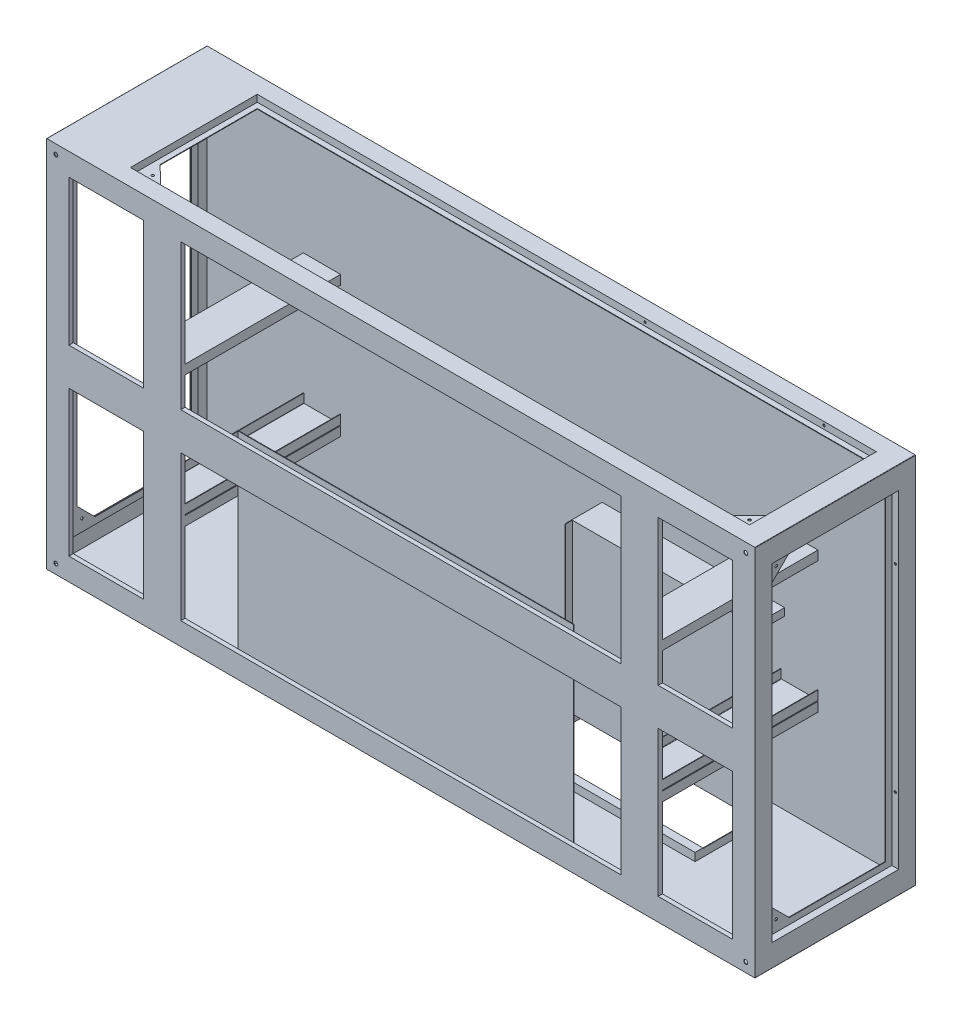
SolidWorks part; units mm, degrees
ref_plane "前视基准面" through (0, 0, 0) normal (0, 0, 1) x (1, 0, 0)
ref_plane "上视基准面" through (0, 0, 0) normal (0, 1, 0) x (1, 0, 0)
ref_plane "右视基准面" through (0, 0, 0) normal (1, 0, 0) x (0, 0, -1)
sketch "草图1" plane through (0, 0, 0) normal (0, 0, 1) x (1, 0, 0)
  line L1 (950, -500) -> (-950, -500)
  line L2 (950, -500) -> (950, 500)
  line L3 (950, 500) -> (-950, 500)
  line L4 (-950, -500) -> (-950, 500)
  line L5 (950, -500) -> (-950, 500) construction
  line L6 (950, 500) -> (-950, -500) construction
  line L7 (948.5, -498.5) -> (-948.5, -498.5)
  line L8 (948.5, -498.5) -> (948.5, 498.5)
  line L9 (948.5, 498.5) -> (-948.5, 498.5)
  line L10 (-948.5, -498.5) -> (-948.5, 498.5)
  line L11 (948.5, -498.5) -> (-948.5, 498.5) construction
  line L12 (948.5, 498.5) -> (-948.5, -498.5) construction
  point P0 (0, 0)
  point P6 (0, 0)
  dimension "D1" = 1.5
  dimension "D2" = 1.5
  dimension "D3" = 1900
  dimension "D4" = 1000
extrude "凸台-拉伸1" add sketch "草图1" along normal mid plane 430
sketch "草图2" plane through (0, 0, -215) normal (0, 0, -1) x (-1, 0, 0)
  line L1 (-950, 500) -> (950, 500)
  line L2 (-950, 500) -> (-950, -500)
  line L3 (-950, -500) -> (950, -500)
  line L4 (950, 500) -> (950, -500)
  line L5 (-950, 500) -> (950, -500) construction
  line L6 (-950, -500) -> (950, 500) construction
  point P0 (0, 0)
extrude "凸台-拉伸2" add sketch "草图2" against normal blind 1.5
sketch "草图3" plane through (-950, 0, 0) normal (-1, 0, 0) x (0, 0, 1)
  line L0 (215, -500) -> (-215, -500) construction
  line L1 (-170, -440) -> (170, -440)
  line L2 (-170, -440) -> (-170, 440)
  line L3 (-170, 440) -> (170, 440)
  line L4 (170, -440) -> (170, 440)
  line L5 (-170, -440) -> (170, 440) construction
  line L6 (-170, 440) -> (170, -440) construction
  line L7 (-215, 500) -> (-215, -500) construction
  point P0 (0, 0)
  dimension "D1" = 60
  dimension "D2" = 45
extrude "切除-拉伸1" cut sketch "草图3" against normal blind 1.5
sketch "草图6" plane through (0, 0, 215) normal (0, 0, 1) x (1, 0, 0)
  line L0 (950, 500) -> (-950, 500) construction
  line L1 (-950, -500) -> (950, -500)
  line L2 (-950, -500) -> (-950, 500)
  line L3 (-950, 500) -> (950, 500)
  line L4 (950, -500) -> (950, 500)
  line L5 (-950, -500) -> (950, 500) construction
  line L6 (-950, 500) -> (950, -500) construction
  line L7 (-950, 500) -> (-950, -500) construction
  point P0 (0, 0)
extrude "凸台-拉伸5" add sketch "草图6" against normal blind 1.5
sketch "草图7" plane through (0, 0, 227) normal (0, 0, 1) x (1, 0, 0)
  line L0 (0, 500) -> (0, -500) construction
  line L1 (-890, -440) -> (-690, -440)
  line L2 (-890, -440) -> (-890, 440)
  line L3 (-890, 440) -> (-690, 440)
  line L4 (-690, -440) -> (-690, 440)
  line L5 (-890, -440) -> (-690, 440) construction
  line L6 (-890, 440) -> (-690, -440) construction
  line L7 (-590, -440) -> (590, -440)
  line L8 (-590, -440) -> (-590, 440)
  line L9 (-590, 440) -> (590, 440)
  line L10 (590, -440) -> (590, 440)
  line L11 (-590, -440) -> (590, 440) construction
  line L12 (-590, 440) -> (590, -440) construction
  line L13 (690, -440) -> (890, -440)
  line L14 (690, -440) -> (690, 440)
  line L15 (690, 440) -> (890, 440)
  line L16 (890, -440) -> (890, 440)
  line L17 (690, -440) -> (890, 440) construction
  line L18 (690, 440) -> (890, -440) construction
  line L19 (945, 500) -> (-945, 500) construction
  line L20 (-945, -500) -> (945, -500) construction
  line L21 (-400, 0) -> (950, 0) construction
  line L22 (-950, 495) -> (-950, -495) construction
  line L23 (950, -495) -> (950, 495) construction
  point P0 (-790, 0)
  point P5 (0, 0)
  point P10 (790, 0)
  dimension "D1" = 60
  dimension "D2" = 60
  dimension "D3" = 60
  dimension "D4" = 60
  dimension "D5" = 100
  dimension "D6" = 200
extrude "切除-拉伸8" cut sketch "草图7" against normal blind 29.5
hole_wizard "Ø10.5 (10.5) 直径孔1" positions "草图9" profile "草图8" hole size "Ø10.5" standard "GB"
sketch "草图9" plane through (0, 0, 215) normal (0, 0, 1) x (1, 0, 0)
  line L0 (950, 500) -> (-950, 500) construction
  line L1 (-950, 500) -> (-950, -500) construction
  line L2 (950, -500) -> (950, 500) construction
  line L3 (-950, -500) -> (950, -500) construction
  point P0 (-925, 475)
  point P2 (925, 475)
  point P4 (-925, -475)
  point P6 (925, -475)
  dimension "D1" = 25
  dimension "D2" = 25
  dimension "D3" = 25
  dimension "D4" = 25
  dimension "D5" = 25
  dimension "D6" = 25
  dimension "D7" = 25
  dimension "D8" = 25
sketch "草图8" plane through (-925, 475, 215) normal (1, 0, 0) x (0, -1, 0)
  line L0 (0, 0) -> (0, 4.6545)
  line L1 (0, 4.6545) -> (5.25, 1.5)
  line L2 (5.25, 1.5) -> (5.25, 0)
  line L5 (5.25, 0) -> (0, 0)
  line L10 (0, 4.6545) -> (-5.25, 1.5) construction
  line L11 (0, -6.35) -> (0, 107.95) construction
  dimension "孔直径" = 10.5
  dimension "孔深度" = 1.5
  dimension "导头角度" = 118
sketch "草图10" plane through (0, 500, 0) normal (0, 1, 0) x (1, 0, 0)
  line L0 (950, -215) -> (950, 215) construction
  line L1 (-770, 170) -> (890, 170)
  line L2 (-770, 170) -> (-770, -170)
  line L3 (-770, -170) -> (890, -170)
  line L4 (890, 170) -> (890, -170)
  line L5 (-770, 170) -> (890, -170) construction
  line L6 (-770, -170) -> (890, 170) construction
  line L7 (945, -215) -> (-945, -215) construction
  line L8 (-950, -215) -> (-950, 215) construction
  line L9 (950, 215) -> (-950, 215) construction
  point P0 (0, 0)
  dimension "D1" = 60
  dimension "D2" = 45
  dimension "D3" = 180
  dimension "D4" = 45
extrude "切除-拉伸9" cut sketch "草图10" against normal blind 1.5
hole_wizard "Ø25.5 (25.5) 直径孔1" positions "草图15" profile "草图14" hole size "Ø25.5" standard "GB"
sketch "草图15" plane through (0, 0, -215) normal (0, 0, -1) x (-1, 0, 0)
  line L0 (-950, 500) -> (950, 500) construction
  line L1 (950, 500) -> (950, -500) construction
  line L2 (-950, -500) -> (-950, 500) construction
  line L3 (950, -500) -> (-950, -500) construction
  point P0 (-900, 450)
  point P2 (-900, -450)
  point P4 (900, -450)
  point P6 (900, 450)
  dimension "D1" = 50
  dimension "D2" = 50
  dimension "D3" = 50
  dimension "D4" = 50
  dimension "D5" = 50
  dimension "D6" = 50
  dimension "D7" = 50
  dimension "D8" = 50
sketch "草图14" plane through (900, 450, -215) normal (1, 0, 0) x (0, 1, 0)
  line L0 (0, 0) -> (0, 19.661)
  line L1 (0, 19.661) -> (12.75, 12)
  line L2 (12.75, 12) -> (12.75, 0)
  line L5 (12.75, 0) -> (0, 0)
  line L10 (0, 19.661) -> (-12.75, 12) construction
  line L11 (0, -6.35) -> (0, 107.95) construction
  dimension "孔直径" = 25.5
  dimension "孔深度" = 12
  dimension "导头角度" = 118
fillet "圆角1" radius 1 4 edges at (950, 500, 0) (-950, 500, 0) (950, -500, 0) (-950, -500, 0)
sketch "草图17" plane through (-948.5, 0, 0) normal (1, 0, 0) x (0, 0, -1)
  line L1 (-171.5, -441.5) -> (171.5, -441.5)
  line L2 (-171.5, -441.5) -> (-171.5, 441.5)
  line L3 (-171.5, 441.5) -> (171.5, 441.5)
  line L4 (171.5, -441.5) -> (171.5, 441.5)
  line L5 (-171.5, -441.5) -> (171.5, 441.5) construction
  line L6 (-171.5, 441.5) -> (171.5, -441.5) construction
  line L7 (-170, -440) -> (170, -440)
  line L8 (-170, -440) -> (-170, 440)
  line L9 (-170, 440) -> (170, 440)
  line L10 (170, -440) -> (170, 440)
  line L11 (-170, -440) -> (170, 440) construction
  line L12 (-170, 440) -> (170, -440) construction
  point P0 (0, 0)
  point P6 (0, 0)
  dimension "D1" = 1.5
  dimension "D2" = 1.5
extrude "凸台-拉伸8" add sketch "草图17" along normal blind 17
sketch "草图18" plane through (-931.5, 0, 0) normal (1, 0, 0) x (0, 0, -1)
  line L1 (-153.5, -423.5) -> (153.5, -423.5)
  line L2 (-153.5, -423.5) -> (-153.5, 423.5)
  line L3 (-153.5, 423.5) -> (153.5, 423.5)
  line L4 (153.5, -423.5) -> (153.5, 423.5)
  line L5 (-153.5, -423.5) -> (153.5, 423.5) construction
  line L6 (-153.5, 423.5) -> (153.5, -423.5) construction
  line L7 (-171.5, -441.5) -> (171.5, -441.5)
  line L8 (-171.5, -441.5) -> (-171.5, 441.5)
  line L9 (-171.5, 441.5) -> (171.5, 441.5)
  line L10 (171.5, -441.5) -> (171.5, 441.5)
  line L11 (-171.5, -441.5) -> (171.5, 441.5) construction
  line L12 (-171.5, 441.5) -> (171.5, -441.5) construction
  point P0 (0, 0)
  point P6 (0, 0)
  dimension "D1" = 18
  dimension "D2" = 18
extrude "凸台-拉伸9" add sketch "草图18" along normal blind 1.5
mirror "镜向5" about plane through (0, 0, 0) normal (1, 0, 0) of "切除-拉伸1"
sketch "草图19" plane through (0, 498.5, 0) normal (0, -1, 0) x (1, 0, 0)
  line L1 (890, 170) -> (-770, 170)
  line L2 (890, 170) -> (890, -170)
  line L3 (890, -170) -> (-770, -170)
  line L4 (-770, 170) -> (-770, -170)
  line L5 (-771.5, -171.5) -> (891.5, -171.5)
  line L6 (-771.5, -171.5) -> (-771.5, 171.5)
  line L7 (-771.5, 171.5) -> (891.5, 171.5)
  line L8 (891.5, -171.5) -> (891.5, 171.5)
  dimension "D1" = 1.5
  dimension "D2" = 1.5
  dimension "D3" = 1.5
  dimension "D4" = 1.5
extrude "凸台-拉伸10" add sketch "草图19" along normal blind 17
sketch "草图20" plane through (0, 481.5, 0) normal (0, -1, 0) x (1, 0, 0)
  line L1 (-771.5, -171.5) -> (891.5, -171.5)
  line L2 (-771.5, -171.5) -> (-771.5, 171.5)
  line L3 (-771.5, 171.5) -> (891.5, 171.5)
  line L4 (891.5, -171.5) -> (891.5, 171.5)
  line L5 (874, 154) -> (-755.5, 154)
  line L6 (874, 154) -> (874, -155.5)
  line L7 (874, -155.5) -> (-755.5, -155.5)
  line L8 (-755.5, 154) -> (-755.5, -155.5)
  dimension "D1" = 16
  dimension "D2" = 16
  dimension "D3" = 17.5
  dimension "D4" = 17.5
extrude "凸台-拉伸11" add sketch "草图20" along normal blind 1.5
mirror "镜向6" about plane through (0, 0, 0) normal (1, 0, 0) of "凸台-拉伸9", "切除-拉伸1", "凸台-拉伸8"
sketch "草图33" plane through (0, 0, 213.5) normal (0, 0, -1) x (-1, 0, 0)
  line L0 (-690, -440) -> (-690, 440) construction
  line L1 (-689, -200) -> (-591, -200)
  line L2 (-690, -199) -> (-690, -175)
  line L3 (-690, -175) -> (-688.5, -175)
  line L4 (-590, -199) -> (-590, -175)
  line L5 (-590, 440) -> (-590, -440) construction
  line L6 (-591.5, -175) -> (-590, -175)
  line L7 (-687.5, -198.5) -> (-592.5, -198.5)
  line L8 (-688.5, -197.5) -> (-688.5, -175)
  line L9 (949, -500) -> (-949, -500) construction
  line L10 (-591.5, -197.5) -> (-591.5, -175)
  line L11 (590, -440) -> (590, 440) construction
  line L12 (590, -175) -> (591.5, -175)
  line L13 (590, -175) -> (590, -199)
  line L14 (591, -200) -> (689, -200)
  line L15 (690, -175) -> (690, -199)
  line L16 (690, 440) -> (690, -440) construction
  line L17 (690, -175) -> (688.5, -175)
  line L18 (-690, 125) -> (-690, 150)
  line L19 (591.5, -175) -> (591.5, -198)
  line L20 (592, -198.5) -> (688, -198.5)
  line L21 (688.5, -175) -> (688.5, -198)
  line L22 (-690, 150) -> (-590, 150)
  line L23 (-590, 150) -> (-590, 125)
  line L24 (-590, 125) -> (-591.5, 125)
  line L25 (-591.5, 125) -> (-591.5, 148.5)
  line L26 (-591.5, 148.5) -> (-688.5, 148.5)
  line L27 (-688.5, 148.5) -> (-688.5, 125)
  line L28 (-688.5, 125) -> (-690, 125)
  line L29 (-949, 500) -> (949, 500) construction
  line L30 (590, 125) -> (590, 150)
  line L31 (590, 150) -> (690, 150)
  line L32 (690, 150) -> (690, 125)
  line L33 (690, 125) -> (688.5, 125)
  line L34 (688.5, 125) -> (688.5, 148.5)
  line L35 (688.5, 148.5) -> (591.5, 148.5)
  line L36 (591.5, 148.5) -> (591.5, 125)
  line L37 (591.5, 125) -> (590, 125)
  line L38 (-690, -226.5) -> (-690, -201.5)
  line L39 (-690, -201.5) -> (-590, -201.5)
  line L40 (-590, -201.5) -> (-590, -226.5)
  line L41 (-590, -226.5) -> (-591.5, -226.5)
  line L42 (-591.5, -226.5) -> (-591.5, -203)
  line L43 (-591.5, -203) -> (-688.5, -203)
  line L44 (-688.5, -203) -> (-688.5, -226.5)
  line L45 (-688.5, -226.5) -> (-690, -226.5)
  line L46 (948.5, 498.5) -> (-948.5, 498.5) construction
  line L47 (590, -226.5) -> (590, -201.5)
  line L48 (590, -201.5) -> (690, -201.5)
  line L49 (690, -201.5) -> (690, -226.5)
  line L50 (690, -226.5) -> (688.5, -226.5)
  line L51 (688.5, -226.5) -> (688.5, -203)
  line L52 (688.5, -203) -> (591.5, -203)
  line L53 (591.5, -203) -> (591.5, -226.5)
  line L54 (591.5, -226.5) -> (590, -226.5)
  arc A0 (-592.5, -198.5) -> (-591.5, -197.5) centre (-592.5, -197.5) ccw
  arc A1 (-687.5, -198.5) -> (-688.5, -197.5) centre (-687.5, -197.5) cw
  arc A2 (-591, -200) -> (-590, -199) centre (-591, -199) ccw
  arc A3 (-689, -200) -> (-690, -199) centre (-689, -199) cw
  arc A4 (688, -198.5) -> (688.5, -198) centre (688, -198) ccw
  arc A5 (591.5, -198) -> (592, -198.5) centre (592, -198) ccw
  arc A6 (689, -200) -> (690, -199) centre (689, -199) ccw
  arc A7 (590, -199) -> (591, -200) centre (591, -199) ccw
  point P20 (-590, -200)
  point P23 (-690, -200)
  point P42 (690, -200)
  point P45 (590, -200)
  dimension "D7" = 1
  dimension "D8" = 1
  dimension "D15" = 0.5
  dimension "D16" = 1
  dimension "D1" = 25
  dimension "D2" = 1.5
  dimension "D3" = 1.5
  dimension "D4" = 1.5
  dimension "D5" = 300
  dimension "D6" = 25
  dimension "D9" = 300
  dimension "D10" = 1.5
  dimension "D11" = 1.5
  dimension "D12" = 1.5
  dimension "D13" = 25
  dimension "D14" = 25
  dimension "D17" = 25
  dimension "D18" = 1.5
  dimension "D19" = 1.5
  dimension "D20" = 1.5
  dimension "D21" = 25
  dimension "D22" = 350
  dimension "D23" = 25
  dimension "D24" = 25
  dimension "D25" = 1.5
  dimension "D26" = 1.5
  dimension "D27" = 1.5
  dimension "D28" = 350
  dimension "D29" = 1.5
  dimension "D30" = 1.5
  dimension "D31" = 1.5
  dimension "D32" = 25
  dimension "D33" = 700
  dimension "D34" = 25
  dimension "D35" = 25
  dimension "D36" = 25
  dimension "D37" = 1.5
  dimension "D38" = 1.5
  dimension "D39" = 1.5
  dimension "D40" = 700
extrude "凸台-拉伸18" add sketch "草图33" along normal up to next
sketch "草图34" plane through (0, -500, 0) normal (0, -1, 0) x (-1, 0, 0)
  line L0 (949, 215) -> (-949, 215) construction
  line L1 (-113, -25) -> (-599, -25)
  line L2 (-113, -25) -> (-113, 155)
  line L3 (-113, 155) -> (-599, 155)
  line L4 (-599, -25) -> (-599, 155)
  line L5 (-949, 215) -> (-949, -215) construction
  dimension "D1" = 486
  dimension "D2" = 180
  dimension "D3" = 60
  dimension "D4" = 350
extrude "切除-拉伸13" cut sketch "草图34" against normal blind 1.5
sketch "草图35" plane through (0, -498.5, 0) normal (0, 1, 0) x (1, 0, 0)
  line L1 (600.5, -26.5) -> (111.5, -26.5)
  line L2 (600.5, -26.5) -> (600.5, 156.5)
  line L3 (600.5, 156.5) -> (111.5, 156.5)
  line L4 (111.5, -26.5) -> (111.5, 156.5)
  line L5 (113, 155) -> (599, 155)
  line L6 (113, 155) -> (113, -25)
  line L7 (113, -25) -> (599, -25)
  line L8 (599, 155) -> (599, -25)
  dimension "D1" = 1.5
  dimension "D2" = 1.5
  dimension "D3" = 1.5
  dimension "D4" = 1.5
extrude "凸台-拉伸19" add sketch "草图35" along normal blind 20
sketch "草图36" plane through (0, -478.5, 0) normal (0, 1, 0) x (1, 0, 0)
  line L0 (600.5, -26.5) -> (600.5, 156.5) construction
  line L1 (600.5, 113.5) -> (599, 113.5)
  line L2 (600.5, 113.5) -> (600.5, 133.5)
  line L3 (600.5, 133.5) -> (111.5, 133.5)
  line L4 (111.5, 113.5) -> (111.5, 133.5)
  line L5 (111.5, 156.5) -> (111.5, -26.5) construction
  line L6 (599, -25) -> (599, 155) construction
  line L7 (599, 132) -> (113, 132)
  line L8 (599, 132) -> (599, 113.5)
  line L10 (113, 132) -> (113, 113.5)
  line L11 (113, 155) -> (113, -25) construction
  line L12 (113, 113.5) -> (111.5, 113.5)
  line L13 (599, 155) -> (113, 155) construction
  dimension "D1" = 20
  dimension "D2" = 1.5
  dimension "D3" = 23
extrude "凸台-拉伸20" add sketch "草图36" along normal blind 450
sketch "草图37" plane through (0, 0, -213.5) normal (0, 0, 1) x (1, 0, 0)
  line L0 (600.5, -48.5) -> (600.5, -28.5)
  line L1 (600.5, -28.5) -> (111.5, -28.5)
  line L2 (111.5, -28.5) -> (111.5, -48.5)
  line L3 (111.5, -48.5) -> (113, -48.5)
  line L4 (113, -48.5) -> (113, -30)
  line L5 (113, -30) -> (599, -30)
  line L6 (599, -30) -> (599, -48.5)
  line L7 (599, -48.5) -> (600.5, -48.5)
  line L8 (600.5, -28.5) -> (600.5, -198.5) construction
  line L9 (111.5, -28.5) -> (111.5, -478.5) construction
  line L10 (600.5, -28.5) -> (111.5, -28.5) construction
  dimension "D1" = 1.5
  dimension "D2" = 1.5
  dimension "D3" = 20
  dimension "D4" = 1.5
  dimension "D5" = 20
extrude "凸台-拉伸21" add sketch "草图37" along normal up to next
sketch "草图38" plane through (0, -478.5, 0) normal (0, 1, 0) x (1, 0, 0)
  line L0 (111.5, 156.5) -> (111.5, 133.5) construction
  line L1 (600.5, 133.5) -> (111.5, 133.5)
  line L2 (600.5, 133.5) -> (600.5, 156.5)
  line L3 (600.5, 156.5) -> (111.5, 156.5)
  line L4 (111.5, 133.5) -> (111.5, 156.5)
  line L5 (600.5, 156.5) -> (111.5, 156.5) construction
extrude "凸台-拉伸22" add sketch "草图38" along normal blind 1.5
sketch "草图39" plane through (0, -478.5, 0) normal (0, 1, 0) x (1, 0, 0)
  line L0 (111.5, 113.5) -> (111.5, -26.5) construction
  line L1 (600.5, -26.5) -> (111.5, -26.5)
  line L2 (600.5, -26.5) -> (600.5, -5.5)
  line L3 (600.5, -5.5) -> (111.5, -5.5)
  line L4 (111.5, -26.5) -> (111.5, -5.5)
  dimension "D1" = 21
extrude "凸台-拉伸23" add sketch "草图39" along normal blind 1.5
sketch "草图41" plane through (-931.5, 0, 0) normal (-1, 0, 0) x (0, 0, 1)
  line L0 (153.5, 423.5) -> (153.5, 375)
  line L1 (153.5, 423.5) -> (153.5, -423.5) construction
  line L2 (153.5, 375) -> (105, 423.5)
  line L3 (-153.5, 423.5) -> (153.5, 423.5) construction
  line L4 (105, 423.5) -> (153.5, 423.5)
  line L5 (-170, 440) -> (170, 440) construction
  line L6 (170, 440) -> (170, -440) construction
  line L7 (153.5, -375) -> (153.5, -423.5)
  line L8 (153.5, -423.5) -> (105, -423.5)
  line L9 (153.5, -423.5) -> (-153.5, -423.5) construction
  line L10 (105, -423.5) -> (153.5, -375)
  line L11 (170, -440) -> (-170, -440) construction
  dimension "D1" = 65
  dimension "D2" = 65
  dimension "D3" = 65
  dimension "D4" = 65
extrude "凸台-拉伸24" add sketch "草图41" against normal blind 1.5
mirror "镜向7" about plane through (0, 0, 0) normal (1, 0, 0) of "凸台-拉伸24"
sketch "草图42" plane through (0, 481.5, 0) normal (0, 1, 0) x (1, 0, 0)
  line L0 (874, -154) -> (825, -154)
  line L1 (874, -154) -> (-755.5, -154) construction
  line L2 (825, -154) -> (874, -105)
  line L3 (874, 155.5) -> (874, -154) construction
  line L4 (874, -105) -> (874, -154)
  line L6 (890, 170) -> (890, -170) construction
  line L7 (890, -170) -> (-770, -170) construction
  line L8 (-755.5, -154) -> (-705, -154)
  line L9 (-705, -154) -> (-755.5, -105)
  line L10 (-755.5, -154) -> (-755.5, 155.5) construction
  line L11 (-755.5, -105) -> (-755.5, -154)
  line L12 (-770, -170) -> (-770, 170) construction
  dimension "D1" = 65
  dimension "D2" = 65
  dimension "D3" = 65
  dimension "D4" = 65
extrude "凸台-拉伸25" add sketch "草图42" against normal blind 1.5
hole_wizard "Ø7.0 (7) 直径孔1" positions "草图44" profile "草图43" hole size "Ø7.0" standard "GB"
sketch "草图44" plane through (0, 481.5, 0) normal (0, 1, 0) x (1, 0, 0)
  line L0 (-770, -170) -> (890, -170) construction
  line L1 (890, 170) -> (890, -170) construction
  line L2 (-770, -170) -> (-770, 170) construction
  point P0 (-740, -140)
  point P2 (860, -140)
  dimension "D1" = 30
  dimension "D2" = 30
  dimension "D3" = 30
  dimension "D4" = 30
sketch "草图43" plane through (-740, 481.5, 140) normal (1, 0, 0) x (0, 0, 1)
  line L0 (0, 0) -> (0, 3.603)
  line L1 (0, 3.603) -> (3.5, 1.5)
  line L2 (3.5, 1.5) -> (3.5, 0)
  line L5 (3.5, 0) -> (0, 0)
  line L10 (0, 3.603) -> (-3.5, 1.5) construction
  line L11 (0, -6.35) -> (0, 107.95) construction
  dimension "孔直径" = 7
  dimension "孔深度" = 1.5
  dimension "导头角度" = 118
hole_wizard "Ø4.6 (4.6) 直径孔2" positions "草图46" profile "草图45" hole size "Ø4.6" standard "GB"
sketch "草图46" plane through (931.5, 0, 0) normal (1, 0, 0) x (0, 0, -1)
  line L0 (170, 440) -> (-170, 440) construction
  line L1 (-170, 440) -> (-170, -440) construction
  line L2 (-170, -440) -> (170, -440) construction
  point P0 (-140, -410)
  point P2 (-140, 410)
  dimension "D1" = 30
  dimension "D2" = 30
  dimension "D3" = 30
  dimension "D4" = 30
sketch "草图45" plane through (931.5, -410, 140) normal (0, 1, 0) x (0, 0, -1)
  line L0 (0, 0) -> (0, 3.603)
  line L1 (0, 3.603) -> (3.5, 1.5)
  line L2 (3.5, 1.5) -> (3.5, 0)
  line L5 (3.5, 0) -> (0, 0)
  line L10 (0, 3.603) -> (-3.5, 1.5) construction
  line L11 (0, -6.35) -> (0, 107.95) construction
  dimension "孔直径" = 7
  dimension "孔深度" = 1.5
  dimension "导头角度" = 118
sketch "草图47" plane through (-931.5, 0, 0) normal (-1, 0, 0) x (0, 0, 1)
  line L0 (170, -440) -> (170, 440) construction
  line L1 (170, -440) -> (-170, -440) construction
  line L2 (170, 440) -> (-170, 440) construction
  line L3 (170, 440) -> (170, -440) construction
  circle A0 centre (140, 410) radius 3.5
  circle A1 centre (140, -410) radius 3.5
  dimension "D1" = 7
  dimension "D4" = 7
  dimension "D2" = 30
  dimension "D3" = 30
  dimension "D5" = 30
  dimension "D6" = 30
extrude "切除-拉伸14" cut sketch "草图47" against normal blind 10 contours A1 | A0
hole_wizard "Ø6.0 (6) 直径孔1" positions "草图49" profile "草图48" hole size "Ø6.0" standard "GB"
sketch "草图49" plane through (0, 0, -170) normal (0, 0, 1) x (1, 0, 0)
  line L0 (890, 481.5) -> (890, 500) construction
  line L1 (890, 500) -> (-770, 500) construction
  point P2 (750, 491)
  point P4 (270, 491)
  dimension "D1" = 140
  dimension "D2" = 620
  dimension "D3" = 9
  dimension "D4" = 9
sketch "草图48" plane through (750, 491, -170) normal (1, 0, 0) x (0, -1, 0)
  line L0 (0, 0) -> (0, 3.8026)
  line L1 (0, 3.8026) -> (3, 2)
  line L2 (3, 2) -> (3, 0)
  line L5 (3, 0) -> (0, 0)
  line L10 (0, 3.8026) -> (-3, 2) construction
  line L11 (0, -6.35) -> (0, 107.95) construction
  dimension "孔直径" = 6
  dimension "孔深度" = 2
  dimension "导头角度" = 118
hole_wizard "Ø6.0 (6) 直径孔2" positions "草图51" profile "草图50" hole size "Ø6.0" standard "GB"
sketch "草图51" plane through (0, 0, -170) normal (0, 0, 1) x (1, 0, 0)
  line L0 (931.5, 440) -> (950, 440) construction
  line L1 (950, 440) -> (950, -440) construction
  line L2 (931.5, -440) -> (950, -440) construction
  point P0 (941, -265)
  point P2 (941, 265)
  dimension "D1" = 175
  dimension "D2" = 9
  dimension "D3" = 9
  dimension "D4" = 175
sketch "草图50" plane through (941, -265, -170) normal (1, 0, 0) x (0, -1, 0)
  line L0 (0, 0) -> (0, 3.8026)
  line L1 (0, 3.8026) -> (3, 2)
  line L2 (3, 2) -> (3, 0)
  line L5 (3, 0) -> (0, 0)
  line L10 (0, 3.8026) -> (-3, 2) construction
  line L11 (0, -6.35) -> (0, 107.95) construction
  dimension "孔直径" = 6
  dimension "孔深度" = 2
  dimension "导头角度" = 118
mirror "镜向8" about plane through (0, 0, 0) normal (1, 0, 0) of "Ø6.0 (6) 直径孔2"
sketch "草图52" plane through (890, 0, 0) normal (-1, 0, 0) x (0, 0, 1)
  line L0 (214.25, 440) -> (214.25, -440) construction
  line L1 (213.5, -50) -> (215, -50)
  line L2 (213.5, -50) -> (213.5, 50)
  line L3 (213.5, 50) -> (215, 50)
  line L4 (215, -50) -> (215, 50)
  line L5 (213.5, -50) -> (215, 50) construction
  line L6 (213.5, 50) -> (215, -50) construction
  line L7 (213.5, 440) -> (215, 440) construction
  line L8 (213.5, -440) -> (215, -440) construction
  line L9 (215, 0) -> (436.6958, 0) construction
  line L10 (215, 0) -> (432.1863, 0) construction
  line L11 (215, -440) -> (215, 440) construction
  point P0 (214.25, 0)
  dimension "D1" = 1.5
  dimension "D2" = 100
extrude "凸台-拉伸26" add sketch "草图52" along normal up to surface (1780 mm away) up to face at (-890, 0, 214.25)
sketch "草图53" plane through (0, 0, 213.5) normal (0, 0, -1) x (-1, 0, 0)
  line L1 (-688.5, -441.5) -> (-891.5, -441.5)
  line L2 (-688.5, -441.5) -> (-688.5, -48.5)
  line L3 (-688.5, -48.5) -> (-891.5, -48.5)
  line L4 (-891.5, -441.5) -> (-891.5, -48.5)
  line L5 (-890, -50) -> (-690, -50)
  line L6 (-890, -50) -> (-890, -440)
  line L7 (-890, -440) -> (-690, -440)
  line L8 (-690, -50) -> (-690, -440)
  line L9 (-688.5, 48.5) -> (-891.5, 48.5)
  line L10 (-688.5, 48.5) -> (-688.5, 441.5)
  line L11 (-688.5, 441.5) -> (-891.5, 441.5)
  line L12 (-891.5, 48.5) -> (-891.5, 441.5)
  line L13 (-890, 440) -> (-690, 440)
  line L14 (-890, 440) -> (-890, 50)
  line L15 (-890, 50) -> (-690, 50)
  line L16 (-690, 440) -> (-690, 50)
  dimension "D1" = 1.5
  dimension "D2" = 1.5
  dimension "D3" = 1.5
  dimension "D4" = 1.5
  dimension "D5" = 1.5
  dimension "D6" = 1.5
  dimension "D7" = 1.5
  dimension "D8" = 1.5
extrude "凸台-拉伸27" add sketch "草图53" along normal blind 10
sketch "草图54" plane through (0, 0, 213.5) normal (0, 0, -1) x (-1, 0, 0)
  line L1 (-590, -440) -> (590, -440)
  line L2 (-590, -440) -> (-590, -50)
  line L3 (-590, -50) -> (590, -50)
  line L4 (590, -440) -> (590, -50)
  line L5 (591.5, -48.5) -> (-591.5, -48.5)
  line L6 (591.5, -48.5) -> (591.5, -441.5)
  line L7 (591.5, -441.5) -> (-591.5, -441.5)
  line L8 (-591.5, -48.5) -> (-591.5, -441.5)
  line L9 (-591.5, 441.5) -> (591.5, 441.5)
  line L10 (-591.5, 441.5) -> (-591.5, 48.5)
  line L11 (-591.5, 48.5) -> (591.5, 48.5)
  line L12 (591.5, 441.5) -> (591.5, 48.5)
  line L13 (590, 50) -> (-590, 50)
  line L14 (590, 50) -> (590, 440)
  line L15 (590, 440) -> (-590, 440)
  line L16 (-590, 50) -> (-590, 440)
  line L17 (891.5, 441.5) -> (688.5, 441.5)
  line L18 (891.5, 441.5) -> (891.5, 48.5)
  line L19 (891.5, 48.5) -> (688.5, 48.5)
  line L20 (688.5, 441.5) -> (688.5, 48.5)
  line L21 (690, 50) -> (890, 50)
  line L22 (690, 50) -> (690, 440)
  line L23 (690, 440) -> (890, 440)
  line L24 (890, 50) -> (890, 440)
  line L25 (690, -50) -> (890, -50)
  line L26 (690, -50) -> (690, -440)
  line L27 (690, -440) -> (890, -440)
  line L28 (890, -50) -> (890, -440)
  line L29 (891.5, -441.5) -> (688.5, -441.5)
  line L30 (891.5, -441.5) -> (891.5, -48.5)
  line L31 (891.5, -48.5) -> (688.5, -48.5)
  line L32 (688.5, -441.5) -> (688.5, -48.5)
  dimension "D1" = 1.5
  dimension "D2" = 1.5
  dimension "D3" = 1.5
  dimension "D4" = 1.5
  dimension "D5" = 1.5
  dimension "D6" = 1.5
  dimension "D7" = 1.5
  dimension "D8" = 1.5
  dimension "D9" = 1.5
  dimension "D10" = 1.5
  dimension "D11" = 1.5
  dimension "D12" = 1.5
  dimension "D13" = 1.5
  dimension "D14" = 1.5
  dimension "D15" = 1.5
  dimension "D16" = 1.5
extrude "凸台-拉伸28" add sketch "草图54" along normal blind 10
chamfer "倒角1" distance 2 angle 45 4 edges at (112.25, -28.5, -113.5) (599.75, -28.5, -113.5)
sketch "草图58" plane through (0, 0, 203.5) normal (0, 0, -1) x (-1, 0, 0)
  line L1 (-451.0142, 65.983) -> (447.917, 65.983)
  line L2 (-451.0142, 65.983) -> (-451.0142, -500)
  line L3 (-451.0142, -500) -> (447.917, -500)
  line L4 (447.917, 65.983) -> (447.917, -500)
  line L5 (949, -500) -> (-949, -500) construction
extrude "凸台-拉伸31" add sketch "草图58" along normal blind 1.5
